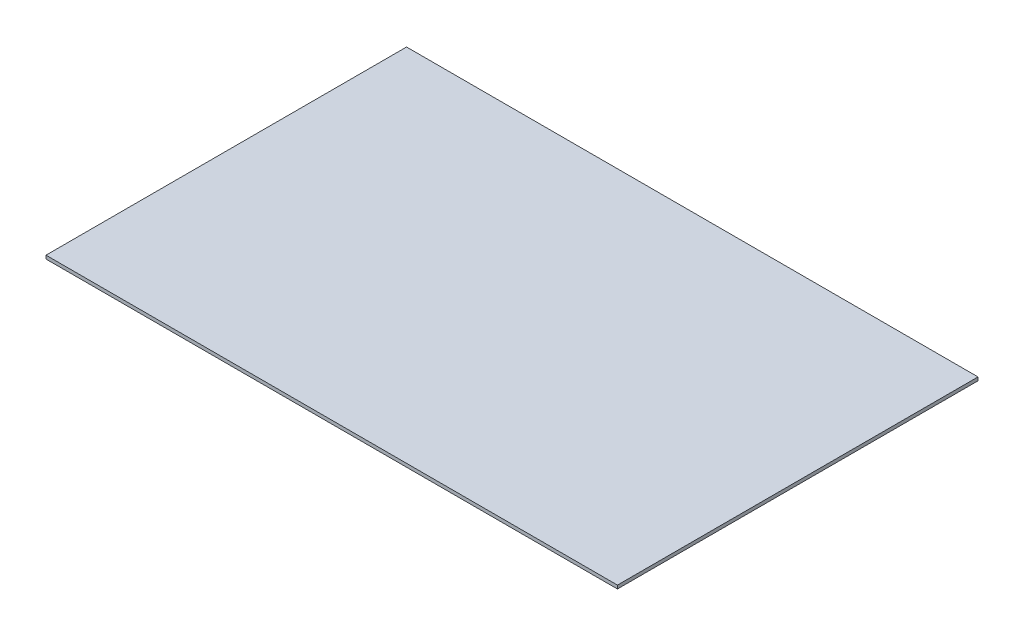
SolidWorks part; units mm, degrees
material "Acrylic (Medium-high impact)"
ref_plane "Front Plane" through (0, 0, 0) normal (0, 0, 1) x (1, 0, 0)
ref_plane "Top Plane" through (0, 0, 0) normal (0, 1, 0) x (1, 0, 0)
ref_plane "Right Plane" through (0, 0, 0) normal (1, 0, 0) x (0, 0, -1)
sketch "Sketch1" plane through (0, 0, 0) normal (0, 1, 0) x (1, 0, 0)
  line L0 (349.25, 336.55) -> (533.4, 336.55)
  line L1 (184.15, 209.55) -> (0, 209.55) construction
  line L2 (0, 0) -> (0, 336.55)
  line L3 (0, 336.55) -> (184.15, 336.55)
  line L4 (533.4, 0) -> (533.4, 336.55)
  line L5 (184.15, 336.55) -> (184.15, 209.55)
  line L6 (184.15, 209.55) -> (349.25, 209.55)
  line L7 (349.25, 336.55) -> (349.25, 209.55)
  line L9 (533.4, 209.55) -> (349.25, 209.55) construction
  line L10 (0, 0) -> (533.4, 0)
  dimension "D1" = 533.4
  dimension "D2" = 336.55
  dimension "D3" = 165.1
  dimension "D4" = 209.55
extrude "Boss-Extrude1" add sketch "Sketch1" along normal blind 3.175
sketch "Sketch2" plane through (0, 3.175, 0) normal (0, 1, 0) x (1, 0, 0)
  line L1 (147.8009, 336.55) -> (409.749, 336.55)
  line L2 (147.8009, 336.55) -> (147.8009, 172.0161)
  line L3 (147.8009, 172.0161) -> (409.749, 172.0161)
  line L4 (409.749, 336.55) -> (409.749, 172.0161)
  line L8 (0, 0) -> (533.4, 0)
  line L9 (533.4, 0) -> (533.4, 336.55)
  line L10 (533.4, 336.55) -> (349.25, 336.55)
  line L11 (349.25, 336.55) -> (349.25, 209.55)
  line L12 (349.25, 209.55) -> (184.15, 209.55)
  line L13 (184.15, 209.55) -> (184.15, 336.55)
  line L14 (184.15, 336.55) -> (0, 336.55)
  line L15 (0, 336.55) -> (0, 0)
  line L16 (0, 0) -> (533.4, 0)
  line L17 (533.4, 0) -> (533.4, 336.55)
  line L18 (533.4, 336.55) -> (349.25, 336.55)
  line L19 (349.25, 336.55) -> (349.25, 209.55)
  line L20 (349.25, 209.55) -> (184.15, 209.55)
  line L21 (184.15, 209.55) -> (184.15, 336.55)
  line L22 (184.15, 336.55) -> (0, 336.55)
  line L23 (0, 336.55) -> (0, 0)
  line M11 (533.4, 336.55) -> (349.25, 336.55)
  line M12 (349.25, 336.55) -> (349.25, 209.55)
  line M13 (349.25, 209.55) -> (184.15, 209.55)
  line M14 (184.15, 209.55) -> (184.15, 336.55)
  line M15 (184.15, 336.55) -> (0, 336.55)
  dimension "D1" = 0
extrude "Boss-Extrude2" add sketch "Sketch2" against normal up to surface (3.175 mm away) contours L4 L2 L3 M11 M12 M13 M14 M15 | L1 M14 M13 M12 up to face at (266.7, 0, -220.6625)
